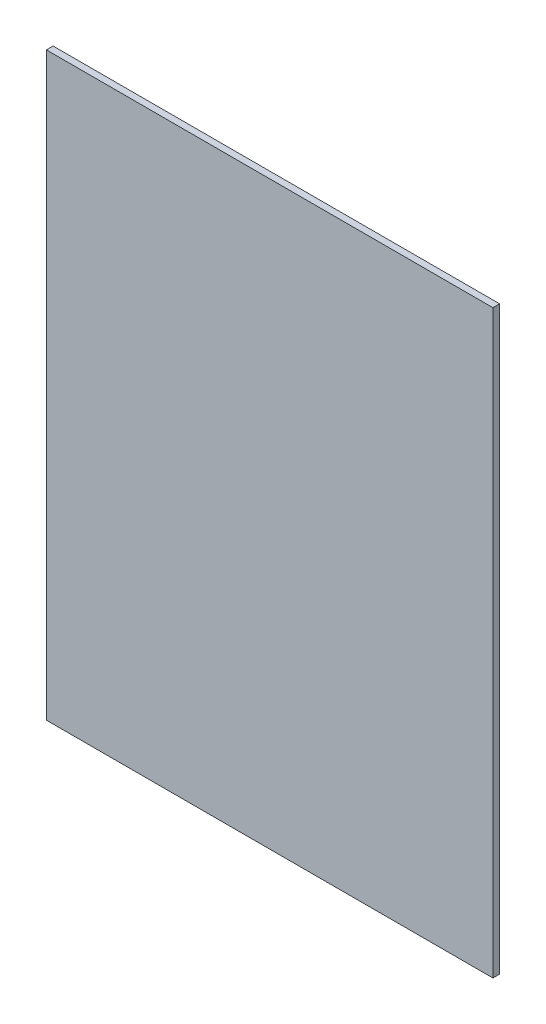
SolidWorks part; units mm, degrees
material "Balsa"
ref_plane "Plano frontal" through (0, 0, 0) normal (0, 0, 1) x (1, 0, 0)
ref_plane "Plano superior" through (0, 0, 0) normal (0, 1, 0) x (1, 0, 0)
ref_plane "Plano direito" through (0, 0, 0) normal (1, 0, 0) x (0, 0, -1)
sketch "Esboço1" plane through (0, 0, 0) normal (0, 0, 1) x (1, 0, 0)
  line L1 (-100, 130) -> (100, 130)
  line L2 (-100, 130) -> (-100, -130)
  line L3 (-100, -130) -> (100, -130)
  line L4 (100, 130) -> (100, -130)
  line L5 (-100, 130) -> (100, -130) construction
  line L6 (-100, -130) -> (100, 130) construction
  point P0 (0, 0)
  dimension "D1" = 200
  dimension "D2" = 260
extrude "Ressalto-extrusão1" add sketch "Esboço1" along normal blind 3
